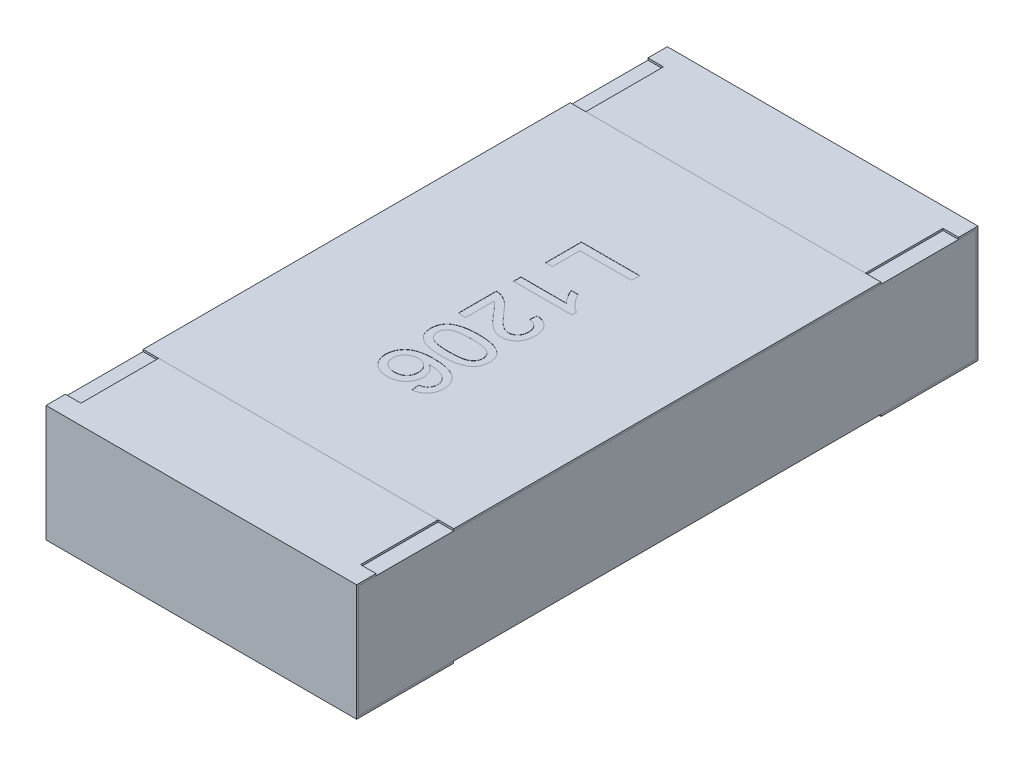
SolidWorks part; units mm, degrees
ref_plane "Front Plane" through (0, 0, 0) normal (0, 0, 1) x (1, 0, 0)
ref_plane "Top Plane" through (0, 0, 0) normal (0, 1, 0) x (1, 0, 0)
ref_plane "Right Plane" through (0, 0, 0) normal (1, 0, 0) x (0, 0, -1)
sketch "Sketch4" plane through (0, 0, 0) normal (1, 0, 0) x (0, 0, -1)
  line L0 (0, 0.1169) -> (0, -0.0721) construction
  line L1 (-1.6, 0) -> (0.3788, 0) construction
  line L2 (-1.6, 0.3) -> (-1.6, -0.3)
  line L3 (-1.6, -0.3) -> (-1.1, -0.3)
  line L4 (-1.1, 0.3) -> (-1.1, 0.29)
  line L5 (-1.1, 0.29) -> (-1.59, 0.29)
  line L6 (-1.59, 0.29) -> (-1.59, -0.29)
  line L7 (-1.59, -0.29) -> (-1.1, -0.29)
  line L8 (-1.1, -0.29) -> (-1.1, -0.3)
  line L9 (-1.1, 0.3) -> (-1.6, 0.3)
  line L10 (1.1, 0.3) -> (1.6, 0.3)
  line L11 (1.1, -0.29) -> (1.1, -0.3)
  line L12 (1.59, -0.29) -> (1.1, -0.29)
  line L13 (1.59, 0.29) -> (1.59, -0.29)
  line L14 (1.1, 0.29) -> (1.59, 0.29)
  line L15 (1.1, 0.3) -> (1.1, 0.29)
  line L16 (1.6, -0.3) -> (1.1, -0.3)
  line L17 (1.6, 0.3) -> (1.6, -0.3)
  dimension "LENGTH" = 1.6
  dimension "HEIGHT" = 0.6
  dimension "END CAP TOP LENGTH" = 0.5
  dimension "END CAP BOTTOM LENGTH" = 0.5
  dimension "D5" = 0.01
  dimension "D6" = 0.01
extrude "Boss-Extrude2" add sketch "Sketch4" along normal mid plane 1.6
sketch "Sketch5" plane through (0, 0, 0) normal (1, 0, 0) x (0, 0, -1)
  line L1 (-1.59, 0.29) -> (1.59, 0.29)
  line L2 (-1.59, 0.29) -> (-1.59, -0.29)
  line L3 (-1.59, -0.29) -> (1.59, -0.29)
  line L4 (1.59, 0.29) -> (1.59, -0.29)
extrude "Boss-Extrude3" add sketch "Sketch5" along normal up to surface and the other way up to surface separate body
sketch "Sketch6" plane through (0, 0.3, 0) normal (0, 1, 0) x (1, 0, 0)
  line L0 (-0.8, 1.6) -> (-0.8, 1.1) construction
  line L1 (-0.8, 1.5) -> (-0.72, 1.5)
  line L2 (-0.8, 1.5) -> (-0.8, 1.1)
  line L3 (-0.8, 1.1) -> (-0.72, 1.1)
  line L4 (-0.72, 1.5) -> (-0.72, 1.1)
  line L5 (0.8, 1.1) -> (-0.8, 1.1) construction
  line L6 (0, 0.0345) -> (0, -0.0345) construction
  line L7 (-0.0325, 0) -> (0.03, 0) construction
  line L8 (0.8, 1.5) -> (0.8, 1.1)
  line L9 (0.8, 1.1) -> (0.72, 1.1)
  line L10 (0.72, 1.5) -> (0.72, 1.1)
  line L11 (0.8, 1.5) -> (0.72, 1.5)
  line L12 (0.8, -1.5) -> (0.72, -1.5)
  line L13 (0.8, -1.5) -> (0.8, -1.1)
  line L14 (0.8, -1.1) -> (0.72, -1.1)
  line L15 (0.72, -1.5) -> (0.72, -1.1)
  line L16 (-0.8, -1.5) -> (-0.72, -1.5)
  line L17 (-0.8, -1.5) -> (-0.8, -1.1)
  line L18 (-0.8, -1.1) -> (-0.72, -1.1)
  line L19 (-0.72, -1.5) -> (-0.72, -1.1)
  dimension "TOP CUT WIDTH" = 0.08
  dimension "TOP CUT LENGTH" = 0.4
extrude "Cut-Extrude1" cut sketch "Sketch6" against normal up to surface (0.01 mm away) up to face at (0, 0.29, 0)
sketch "Sketch7" plane through (0, 0.29, 0) normal (0, 1, 0) x (1, 0, 0)
  line L1 (-0.8, 1.1) -> (0.8, 1.1)
  line L2 (-0.8, 1.1) -> (-0.8, -1.1)
  line L3 (-0.8, -1.1) -> (0.8, -1.1)
  line L4 (0.8, 1.1) -> (0.8, -1.1)
  line L5 (0.72, -1.1) -> (-0.72, -1.1) construction
  line L6 (0.72, 1.1) -> (-0.72, 1.1) construction
  line L7 (-0.8, -1.59) -> (-0.8, 1.59) construction
  line L8 (0.8, 1.59) -> (0.8, -1.59) construction
extrude "Boss-Extrude4" add sketch "Sketch7" along normal up to surface (0.01 mm away) separate body up to face at (0, 0.3, -1.425)
sketch "Sketch12" plane through (0, 0.3, 0) normal (0, 1, 0) x (1, 0, 0)
  line L0 (-0.15, 0.5423) -> (-0.15, -0.5423) construction
  line L1 (0, 0) -> (-0.15, 0) construction
  text T0 "L1206" font "Arial" height 0.3
  dimension "D1" = 0.15
extrude "TEXT1206" cut sketch "Sketch12" against normal blind 0.001
